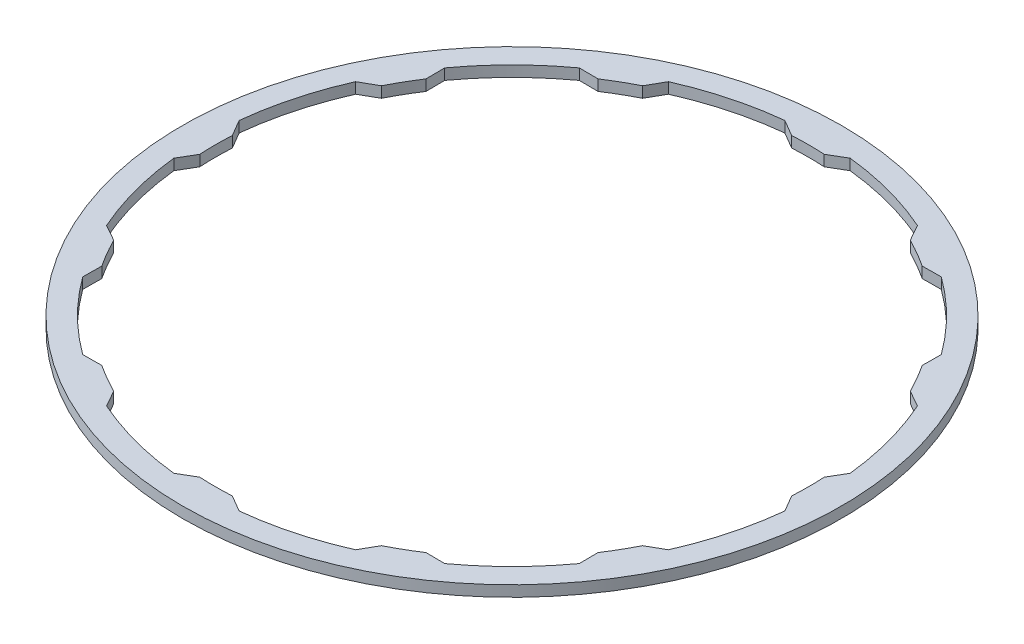
SolidWorks part; units mm, degrees
ref_plane "Front Plane" through (0, 0, 0) normal (0, 0, 1) x (1, 0, 0)
ref_plane "Top Plane" through (0, 0, 0) normal (0, 1, 0) x (1, 0, 0)
ref_plane "Right Plane" through (0, 0, 0) normal (1, 0, 0) x (0, 0, -1)
sketch "Sketch1" plane through (0, 0, 0) normal (0, 1, 0) x (1, 0, 0)
  line L0 (0, 0) -> (0, 17.609) construction
  line L1 (-1.524, 17.609) -> (1.524, 17.609) construction
  line L2 (-0.762, 16.3045) -> (0.762, 16.3045) construction
  line L3 (-0.762, 16.3045) -> (-0.762, 13.822) construction
  line L4 (0.762, 16.3045) -> (0.762, 13.822) construction
  line L5 (-1.524, 17.609) -> (-1.524, 14.2699) construction
  line L6 (1.524, 17.609) -> (1.524, 14.2699) construction
  line L7 (-1.524, 14.2699) -> (-0.762, 13.822)
  line L8 (0.762, 13.822) -> (1.524, 14.2699)
  line L9 (7.5709, 11.5892) -> (8.4547, 11.5961)
  line L10 (5.8151, 13.1201) -> (6.2511, 12.3512)
  line L11 (0, 0) -> (8.8045, 15.2498) construction
  line L12 (12.3512, 6.2511) -> (13.1201, 5.8151)
  line L13 (11.5961, 8.4547) -> (11.5892, 7.5709)
  line L14 (0, 0) -> (15.2498, 8.8045) construction
  line L15 (13.822, -0.762) -> (14.2699, -1.524)
  line L16 (14.2699, 1.524) -> (13.822, 0.762)
  line L17 (0, 0) -> (17.609, 0) construction
  line L18 (11.5892, -7.5709) -> (11.5961, -8.4547)
  line L19 (13.1201, -5.8151) -> (12.3512, -6.2511)
  line L20 (0, 0) -> (15.2498, -8.8045) construction
  line L21 (6.2511, -12.3512) -> (5.8151, -13.1201)
  line L22 (8.4547, -11.5961) -> (7.5709, -11.5892)
  line L23 (0, 0) -> (8.8045, -15.2498) construction
  line L24 (-0.762, -13.822) -> (-1.524, -14.2699)
  line L25 (1.524, -14.2699) -> (0.762, -13.822)
  line L26 (0, 0) -> (0, -17.609) construction
  line L27 (-7.5709, -11.5892) -> (-8.4547, -11.5961)
  line L28 (-5.8151, -13.1201) -> (-6.2511, -12.3512)
  line L29 (0, 0) -> (-8.8045, -15.2498) construction
  line L30 (-12.3512, -6.2511) -> (-13.1201, -5.8151)
  line L31 (-11.5961, -8.4547) -> (-11.5892, -7.5709)
  line L32 (0, 0) -> (-15.2498, -8.8045) construction
  line L33 (-13.822, 0.762) -> (-14.2699, 1.524)
  line L34 (-14.2699, -1.524) -> (-13.822, -0.762)
  line L35 (0, 0) -> (-17.609, 0) construction
  line L36 (-11.5892, 7.5709) -> (-11.5961, 8.4547)
  line L37 (-13.1201, 5.8151) -> (-12.3512, 6.2511)
  line L38 (0, 0) -> (-15.2498, 8.8045) construction
  line L39 (-6.2511, 12.3512) -> (-5.8151, 13.1201)
  line L40 (-8.4547, 11.5961) -> (-7.5709, 11.5892)
  line L41 (0, 0) -> (-8.8045, 15.2498) construction
  circle A0 centre (0, 0) radius 15.3924
  arc A1 (-6.2511, 12.3512) -> (-7.5709, 11.5892) centre (0, 0) ccw
  arc A2 (-1.524, 14.2699) -> (-5.8151, 13.1201) centre (0, 0) ccw
  arc A3 (-11.5892, 7.5709) -> (-12.3512, 6.2511) centre (0, 0) ccw
  arc A4 (0.762, 13.822) -> (-0.762, 13.822) centre (0, 0) ccw
  arc A5 (7.5709, 11.5892) -> (6.2511, 12.3512) centre (0, 0) ccw
  arc A6 (12.3512, 6.2511) -> (11.5892, 7.5709) centre (0, 0) ccw
  arc A7 (-13.822, 0.762) -> (-13.822, -0.762) centre (0, 0) ccw
  arc A8 (-12.3512, -6.2511) -> (-11.5892, -7.5709) centre (0, 0) ccw
  arc A9 (-7.5709, -11.5892) -> (-6.2511, -12.3512) centre (0, 0) ccw
  arc A10 (-0.762, -13.822) -> (0.762, -13.822) centre (0, 0) ccw
  arc A11 (6.2511, -12.3512) -> (7.5709, -11.5892) centre (0, 0) ccw
  arc A12 (11.5892, -7.5709) -> (12.3512, -6.2511) centre (0, 0) ccw
  arc A13 (13.822, -0.762) -> (13.822, 0.762) centre (0, 0) ccw
  arc A14 (5.8151, 13.1201) -> (1.524, 14.2699) centre (0, 0) ccw
  arc A15 (11.5961, 8.4547) -> (8.4547, 11.5961) centre (0, 0) ccw
  arc A16 (14.2699, 1.524) -> (13.1201, 5.8151) centre (0, 0) ccw
  arc A17 (13.1201, -5.8151) -> (14.2699, -1.524) centre (0, 0) ccw
  arc A18 (8.4547, -11.5961) -> (11.5961, -8.4547) centre (0, 0) ccw
  arc A19 (1.524, -14.2699) -> (5.8151, -13.1201) centre (0, 0) ccw
  arc A20 (-5.8151, -13.1201) -> (-1.524, -14.2699) centre (0, 0) ccw
  arc A21 (-11.5961, -8.4547) -> (-8.4547, -11.5961) centre (0, 0) ccw
  arc A22 (-14.2699, -1.524) -> (-13.1201, -5.8151) centre (0, 0) ccw
  arc A23 (-13.1201, 5.8151) -> (-14.2699, 1.524) centre (0, 0) ccw
  arc A24 (-8.4547, 11.5961) -> (-11.5961, 8.4547) centre (0, 0) ccw
  point P5 (0, -15.3924)
  point P6 (0, -13.843)
  point P12 (0, 16.3045)
  dimension "D1" = 30.7848
  dimension "D2" = 27.686
  dimension "D3" = 28.702
  dimension "D4" = 1.5494
  dimension "D5" = 3.048
  dimension "D6" = 1.524
  dimension "D8" = 30
  dimension "D7" = 12
extrude "Boss-Extrude1" add sketch "Sketch1" along normal blind 0.508
